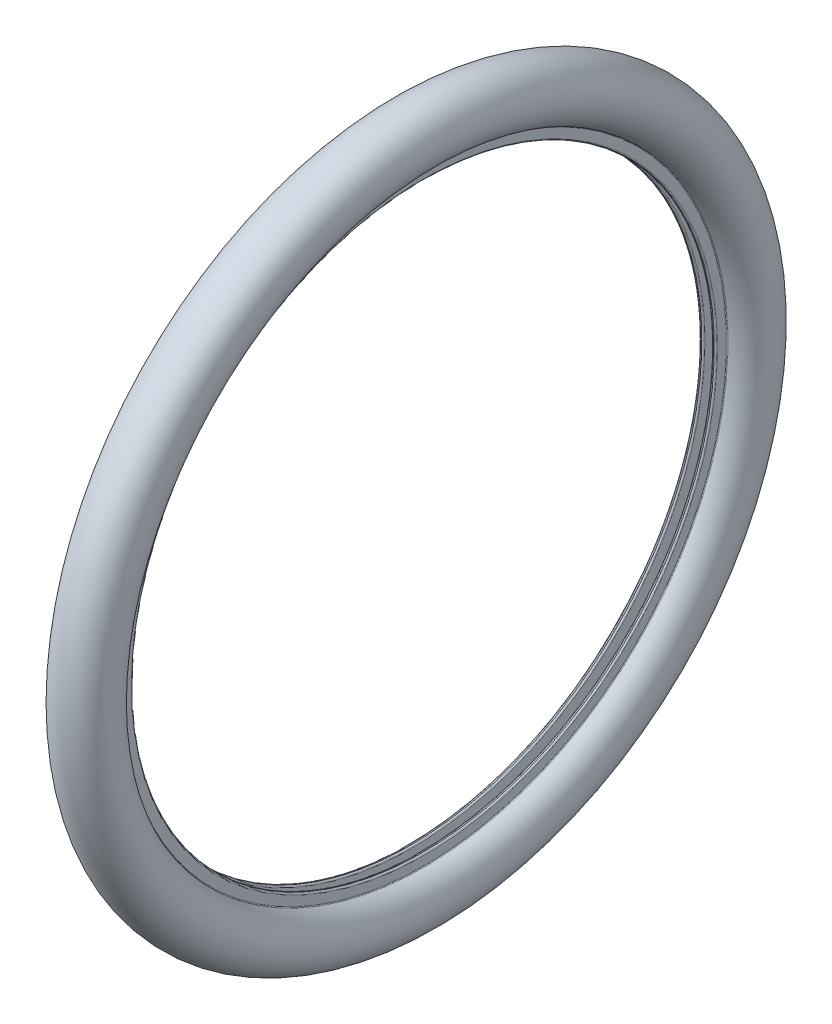
SolidWorks part; units mm, degrees
ref_plane "Спереди" through (0, 0, 0) normal (0, 0, 1) x (1, 0, 0)
ref_plane "Сверху" through (0, 0, 0) normal (0, 1, 0) x (1, 0, 0)
ref_plane "Справа" through (0, 0, 0) normal (1, 0, 0) x (0, 0, -1)
sketch "Эскиз1" plane through (0, 0, 0) normal (0, 0, 1) x (1, 0, 0)
  line L0 (0, 0) -> (0, 290) construction
  line L1 (-8, 282) -> (8, 282) construction
  line L3 (-8, 292.2181) -> (-8, 283.5)
  line L4 (-6.5, 282) -> (-5.5, 282)
  line L5 (-4, 283.5) -> (-4, 297.9061)
  line L6 (-7.5, 301.4061) -> (-8, 301.4061)
  line L7 (8, 292.2181) -> (8, 283.5)
  line L8 (6.5, 282) -> (5.5, 282)
  line L9 (4, 283.5) -> (4, 297.9061)
  line L10 (7.5, 301.4061) -> (8, 301.4061)
  arc A0 (4, 297.9061) -> (7.5, 301.4061) centre (7.5, 297.9061) cw
  arc A1 (-8, 301.4061) -> (8, 301.4061) centre (0, 319.1895) cw
  arc A2 (-8.6198, 293.0754) -> (8.6198, 293.0754) centre (0, 319.1895) cw
  arc A3 (-4, 297.9061) -> (-7.5, 301.4061) centre (-7.5, 297.9061) ccw
  arc A4 (6.5, 282) -> (8, 283.5) centre (6.5, 283.5) ccw
  arc A5 (5.5, 282) -> (4, 283.5) centre (5.5, 283.5) cw
  arc A6 (-4, 283.5) -> (-5.5, 282) centre (-5.5, 283.5) cw
  arc A7 (-6.5, 282) -> (-8, 283.5) centre (-6.5, 283.5) cw
  arc A8 (-8.6198, 293.0754) -> (-8, 292.2181) centre (-8.9028, 292.2181) cw
  arc A9 (8, 292.2181) -> (8.6198, 293.0754) centre (8.9028, 292.2181) cw
  point P6 (0, 346.6895)
  point P8 (0, 282)
  point P19 (4, 301.4061)
  point P22 (-4, 301.4061)
  point P28 (4, 282)
  point P31 (-4, 282)
  point P37 (-8, 292.8789)
  point P40 (8, 292.8789)
  dimension "D3" = 3.5
  dimension "D5" = 1.5
  dimension "D6" = 0.9028
  dimension "D7" = 0.9028
  dimension "D9" = 27.5
  dimension "D10" = 290
  dimension "D8" = 8
  dimension "D1" = 16
  dimension "D2" = 8
  dimension "D4" = 346.6895
sketch "Эскиз3" plane through (0, 0, 0) normal (0, 0, 1) x (1, 0, 0)
  line L0 (-25, 0) -> (25, 0)
  point P6 (0, 0)
revolve "Повернуть1" add sketch "Эскиз1" angle 360 about L0
